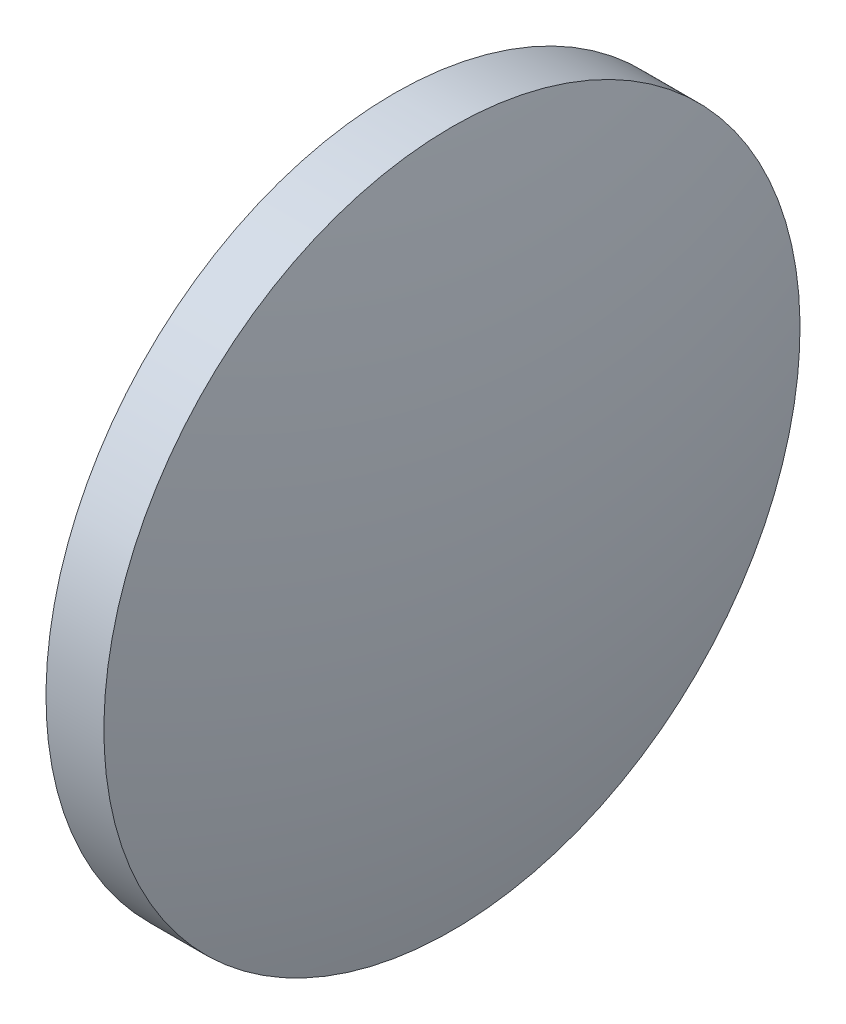
SolidWorks part; units mm, degrees
ref_plane "前视基准面" through (0, 0, 0) normal (0, 0, 1) x (1, 0, 0)
ref_plane "上视基准面" through (0, 0, 0) normal (0, 1, 0) x (1, 0, 0)
ref_plane "右视基准面" through (0, 0, 0) normal (1, 0, 0) x (0, 0, -1)
sketch "草图2" plane through (0, 0, 0) normal (0, 0, 1) x (1, 0, 0)
  line L0 (42.0283, 30.1753) -> (43.0683, 30.1753)
  line L1 (43.0683, 30.1753) -> (43.0683, 17.6753)
  line L2 (43.0683, 17.6753) -> (42.0283, 17.6753)
  line L3 (42.0283, 17.6753) -> (42.0283, 30.1753)
  line L4 (45.143, 23.9253) -> (39.8867, 23.9253) construction
  arc A0 (42.0283, 30.1753) -> (42.0283, 17.6753) centre (66.6784, 23.9253) ccw
  arc A1 (43.0683, 17.6753) -> (43.0683, 30.1753) centre (18.4183, 23.9253) ccw
  dimension "D1" = 1.04
  dimension "D2" = 12.5
revolve "旋转1" add sketch "草图2" angle 360 about L4
